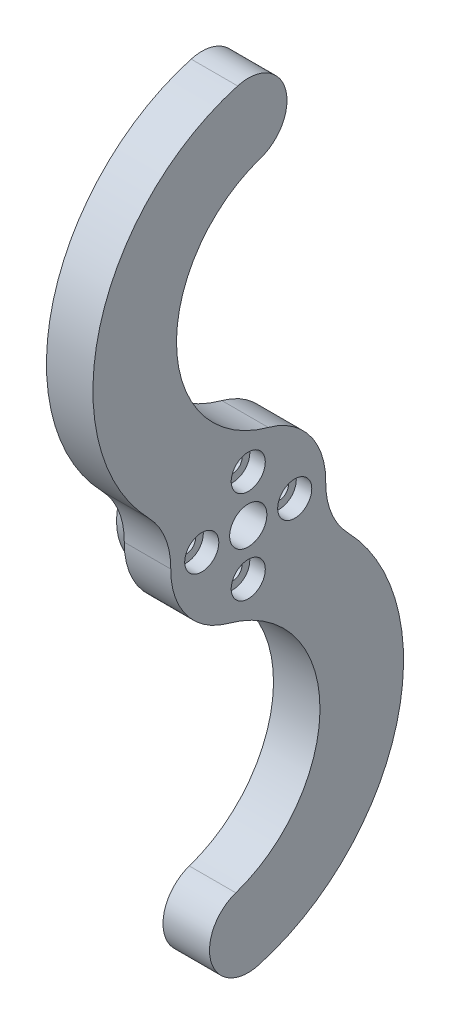
SolidWorks part; units mm, degrees
ref_plane "Front" through (0, 0, 0) normal (0, 0, 1) x (1, 0, 0)
ref_plane "Top" through (0, 0, 0) normal (0, 1, 0) x (1, 0, 0)
ref_plane "Right" through (0, 0, 0) normal (1, 0, 0) x (0, 0, -1)
sketch "Sketch1" plane through (0, 0, 0) normal (1, 0, 0) x (0, 0, -1)
  line L0 (0, 0) -> (9.1396, -4.0581) construction
  arc A0 (9.1396, -4.0581) -> (2.5924, 9.6581) centre (0, 0) ccw
  circle A1 centre (0, 0) radius 50 construction
  arc A2 (-1.6048, -40.2646) -> (1.3676, -49.8093) centre (0, -45) ccw
  arc A6 (-1.6048, -40.2646) -> (-2.5924, -9.6581) centre (-6.7403, -25.1111) ccw
  circle A12 centre (0, 0) radius 2.4
  arc A18 (1.3676, -49.8093) -> (9.1396, -4.0581) centre (-5.6647, -25.079) ccw
  arc A19 (1.6048, 40.2646) -> (2.5924, 9.6581) centre (6.7403, 25.1111) ccw
  arc A20 (-1.3676, 49.8093) -> (-9.1396, 4.0581) centre (5.6647, 25.079) ccw
  arc A21 (1.6048, 40.2646) -> (-1.3676, 49.8093) centre (0, 45) ccw
  arc A22 (-9.1396, 4.0581) -> (-2.5924, -9.6581) centre (0, 0) ccw
  dimension "D1" = 20
  dimension "D2" = 100
  dimension "D3" = 10
  dimension "D4" = 16
  dimension "D5" = 2
  dimension "D7" = 4.8
  dimension "D6" = 13
extrude "Boss-Extrude1" add sketch "Sketch1" along normal blind 6
sketch "Sketch2" plane through (0, 0, 0) normal (-1, 0, 0) x (0, 0, 1)
  circle A0 centre (0, 0) radius 8
  circle A1 centre (0, 0) radius 2.4 construction
  circle A2 centre (0, 0) radius 2.4
  dimension "D1" = 16
extrude "Boss-Extrude2" add sketch "Sketch2" along normal blind 3
hole_wizard "CBORE for M2 SHCS1" positions "Sketch3" profile "Sketch4" counterbore size "M2" standard "ANSI Metric" end condition through all
sketch "Sketch3" plane through (6, 0, 0) normal (1, 0, 0) x (0, 0, -1)
  line L0 (0, 0) -> (0, -6) construction
  circle A0 centre (0, 0) radius 6 construction
  point P0 (0, -6)
  point P6 (-6, 0)
  point P7 (0, 6)
  point P8 (6, 0)
  dimension "D2" = 12
  dimension "D1" = 4
sketch "Sketch4" plane through (6, -6, 0) normal (0, 1, 0) x (0, 0, -1)
  line L0 (0, 0) -> (0, 9)
  line L1 (0, 9) -> (1.2, 9)
  line L3 (1.2, 9) -> (1.2, 2)
  line L4 (1.2, 2) -> (2.2, 2)
  line L5 (2.2, 2) -> (2.2, 0)
  line L7 (2.2, 0) -> (0, 0)
  line L11 (0, -6.35) -> (0, 107.95) construction
  dimension "Thru Hole Dia." = 2.4
  dimension "Thru Hole Depth" = 9
  dimension "C'Bore Dia." = 4.4
  dimension "C'Bore Depth" = 2
fillet "Fillet1" radius 10 2 edges at (3, -4.0581, -9.1396) (3, 4.0581, 9.1396)
